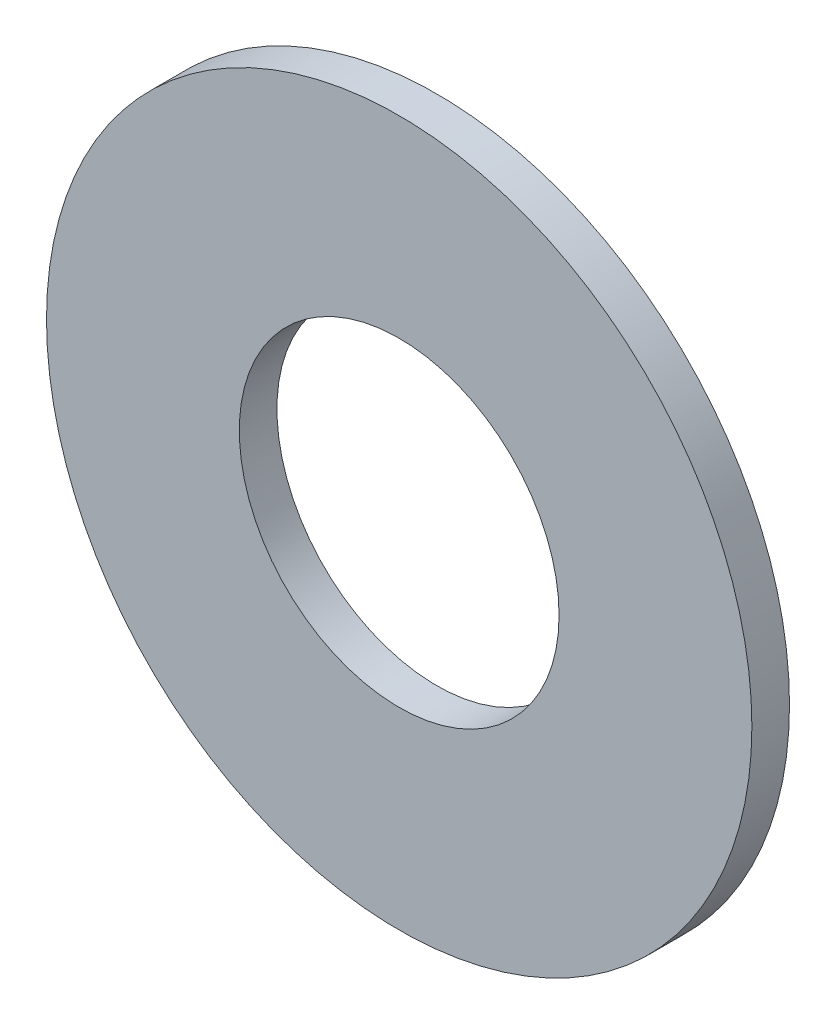
SolidWorks part; units mm, degrees
material "6061-T6 (SS)"
ref_plane "Front Plane" through (0, 0, 0) normal (0, 0, 1) x (1, 0, 0)
ref_plane "Top Plane" through (0, 0, 0) normal (0, 1, 0) x (1, 0, 0)
ref_plane "Right Plane" through (0, 0, 0) normal (1, 0, 0) x (0, 0, -1)
sketch "Sketch1" plane through (0, 0, 0) normal (0, 0, 1) x (1, 0, 0)
  circle A0 centre (0, 0) radius 2.159
  circle A1 centre (0, 0) radius 4.7625
  dimension "ID" = 4.318
  dimension "OD" = 9.525
extrude "Extrude1" add sketch "Sketch1" against normal blind 0.508
